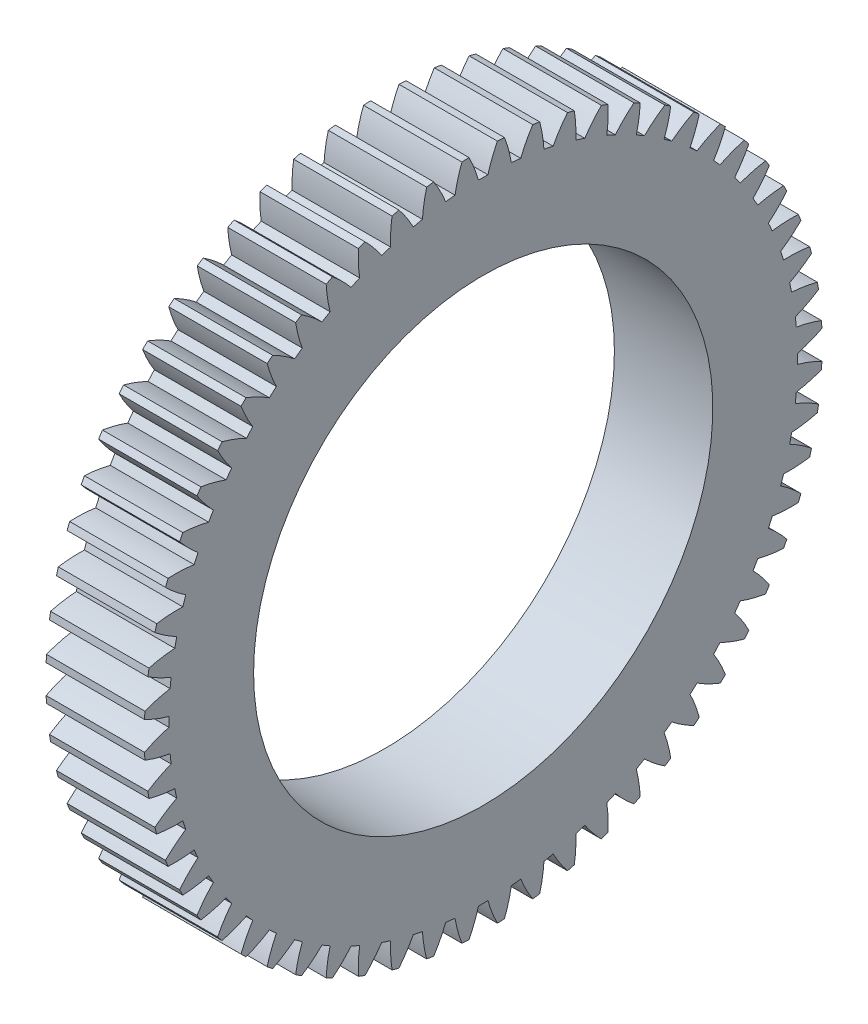
SolidWorks part; units mm, degrees
ref_plane "Plane1" through (0, 0, 0) normal (0, 0, 1) x (1, 0, 0)
ref_plane "Plane2" through (0, 0, 0) normal (0, 1, 0) x (1, 0, 0)
ref_plane "Plane3" through (0, 0, 0) normal (1, 0, 0) x (0, 0, -1)
sketch "HoldingSke" plane through (0, 0, 0) normal (0, 1, 0) x (1, 0, 0)
  line L0 (0, 0) -> (0.5, -0.866)
  line L1 (-15, 0) -> (100, 0) construction
  line L2 (0, 0) -> (-2.1039, 2.3779)
  line L3 (0, 0) -> (-11.863, 4.5341)
  line L4 (0, 0) -> (4.318, 7.479)
  line L5 (0, 0) -> (-46.8476, -17.4728)
  line L6 (0, 0) -> (-7.4607, -5.0337)
  line L7 (-2.1039, 2.3779) -> (8.6586, 51.2059)
  line L8 (-76.2, 54.61) -> (-72.9, 54.61)
  line L9 (-71.009, 38.7566) -> (-53.1078, 45.2721)
  line L10 (-76.2, 71.12) -> (104.1128, 71.12)
  line L11 (0, 0) -> (-9, 0)
  line L12 (-76.2, 101.6) -> (-76.162, 101.6)
  line L13 (24.9733, 27.94) -> (52.9518, 28.4284)
  line L14 (24.9733, 27.94) -> (24.9743, 27.94)
  line L15 (24.9733, 27.94) -> (100.4006, 29.5858)
  line L16 (-63.627, -1) -> (-12.827, -1)
  circle A0 centre (0, 0) radius 21
  circle A1 centre (0, 0) radius 28.749
  circle A2 centre (0, 0) radius 37.5
  circle A3 centre (0, 0) radius 21
  dimension "MHD" = 57.498
  dimension "Hub_dia" = 75
  dimension "Bore" = 42
  dimension "MBD" = 42
  dimension "Num_teeth" = 60
  dimension "Pitch" = 1
  dimension "Overall_len" = 50
  dimension "Show_teeth" = 60
  dimension "Thickness" = 9
  dimension "OAL" = 50.0001
  dimension "T_dim" = 3.3
  dimension "Ap" = 20
  dimension "H" = 19.05
  dimension "Pitch_radius" = 180.3128
  dimension "Width" = 9
  dimension "Backlash" = 0.038
  dimension "Addendum_fac" = 1
  dimension "Dedendum_fac" = 1.25
  dimension "Clearance_fac" = 0.25
  dimension "Dedendum_add" = 0.001
  dimension "Module" = 1
sketch "BasProSke" plane through (0, 0, 0) normal (0, 1, 0) x (1, 0, 0)
  line L0 (-10, 0) -> (60, 0) construction
  line L1 (0, 0) -> (0, 31)
  line L2 (0, 0) -> (9, 0)
  line L3 (9, 0) -> (9, 31)
  line L4 (9, 31) -> (0, 31)
  dimension "Thickness" = 9
  dimension "Diameter" = 62
revolve "Base-Revolve" add sketch "BasProSke" angle 360 about L0
sketch "TooCutSke" plane through (0, 0, 0) normal (1, 0, 0) x (0, 0, -1)
  line L1 (0, 0) -> (0, 107) construction
  line L2 (0, 0) -> (-0.8518, 29.9879) construction
  line L3 (0, 0) -> (-3.1393, 59.9006) construction
  line L4 (-0.8518, 29.9879) -> (-1.5696, 29.9503) construction
  arc A0 (0.4302, 28.7458) -> (-0.4302, 28.7458) centre (0, 0) ccw
  arc A1 (1.3127, 30.9976) -> (-1.3127, 30.9976) centre (0, 0) ccw
  circle A2 centre (0, 0) radius 30 construction
  circle A3 centre (0, 0) radius 28.1908 construction
  arc A4 (-0.4302, 28.7458) -> (-1.3127, 30.9976) centre (-11.9871, 25.5153) ccw
  arc A5 (1.3127, 30.9976) -> (0.4302, 28.7458) centre (11.9871, 25.5153) ccw
  dimension "Root_dia" = 57.498
  dimension "Overcut_dia" = 62.0508
  dimension "Pitch_dia" = 60
  dimension "Base_dia" = 56.3816
  dimension "Flank_rad" = 12
  dimension "Half_ang" = 3
  dimension "Half_CT" = 0.7188
extrude "ToothCut" cut sketch "TooCutSke" along normal through all
fillet "Breaks" [suppressed] radius 0.02
fillet "RootFillets" [suppressed] radius 0.251
pattern_circular "TeethCuts" count 60 every 6 about axis through (-10, 0, 0) along (1, 0, 0) of "ToothCut", "RootFillets", "Breaks"
sketch "HubNeaOneSke" plane through (0, 0, 0) normal (-1, 0, 0) x (0, 0, 1)
  circle A0 centre (0, 0) radius 28.749
  dimension "Diameter" = 57.498
extrude "HubNearOne" [suppressed] add sketch "HubNeaOneSke" along normal blind 41.0001
sketch "HubNeaBotSke" plane through (0, 0, 0) normal (-1, 0, 0) x (0, 0, 1)
  circle A0 centre (0, 0) radius 28.749
  dimension "Diameter" = 57.498
extrude "HubNearBoth" [suppressed] add sketch "HubNeaBotSke" along normal blind 20.5
ref_plane "FarPln" through (9, 0, 0) normal (1, 0, 0) x (0, 0, -1)
sketch "HubFarSke" plane through (9, 0, 0) normal (1, 0, 0) x (0, 0, -1)
  circle A0 centre (0, 0) radius 28.749
  dimension "Diameter" = 57.498
extrude "HubFar" [suppressed] add sketch "HubFarSke" along normal blind 20.5
sketch "BorSke" plane through (0, 0, 0) normal (1, 0, 0) x (0, 0, -1)
  circle A0 centre (0, 0) radius 21
  dimension "Diameter" = 42
extrude "Bore" cut sketch "BorSke" along normal mid plane 100.0001
sketch "KeySke" plane through (0, 0, 0) normal (1, 0, 0) x (0, 0, -1)
  line L0 (-6, 0) -> (-6, 24.3)
  line L1 (-6, 24.3) -> (6, 24.3)
  line L2 (6, 24.3) -> (6, 0)
  line L3 (0, 0) -> (0, 34) construction
  line L4 (-6, 0) -> (6, 0)
  dimension "Offset" = 24.3
  dimension "Width" = 12
extrude "Keyway" [suppressed] cut sketch "KeySke" along normal mid plane 100.0001
pattern_circular "Keyway2" [suppressed] count 2 every 90 about axis through (-10, 0, 0) along (1, 0, 0)
equation "' \"Module@HoldingSke\" = 6.35"
equation "' \"Num_teeth@HoldingSke\" = 12"
equation "' \"Ap@HoldingSke\" =  20"
equation "' \"Ap@HoldingSke\" = 20"
equation "' \"Width@HoldingSke\" = 0.5 * 25.4"
equation "' \"Hub_dia@HoldingSke\"= 1 * 25.4"
equation "' \"Hub_dia@HoldingSke\" = 1 * 25.4"
equation "' \"Overall_len@HoldingSke\" = 1.0 * 25.4"
equation "' \"Bore@HoldingSke\" = 0.75 * 25.4"
equation "' \"T_dim@HoldingSke\" = 0.1 * 25.4"
equation "' \"Width@KeySke\" = 0.25 * 25.4"
equation "' \"Show_teeth@HoldingSke\" = 13"
equation "' \"Backlash@HoldingSke\" = 0.009 * 25.4"
equation "' \"Addendum_fac@HoldingSke\" = 1.0"
equation "' \"Dedendum_fac@HoldingSke\" = 1.25"
equation "' \"Dedendum_add@HoldingSke\" = 0.00005 * 25.4"
equation "' \"Clearance_fac@HoldingSke\" = 0.25"
equation "\"Pitch@HoldingSke\" = 1 / \"Module@HoldingSke\""
equation "\"Overcut_dia@TooCutSke\" = (\"Num_teeth@HoldingSke\" + 2 * \"Addendum_fac@HoldingSke\") / \"Pitch@HoldingSke\" + 0.002 * 25.4"
equation "\"Pitch_dia@TooCutSke\" = \"Num_teeth@HoldingSke\" / \"Pitch@HoldingSke\""
equation "\"Base_dia@TooCutSke\" = \"Num_teeth@HoldingSke\" / \"Pitch@HoldingSke\" * cos((\"Ap@HoldingSke\"  * 3.14159265 / 180))"
equation "\"Root_dia@TooCutSke\" = (\"Num_teeth@HoldingSke\" + 2) / \"Pitch@HoldingSke\" - 2 * (\"Addendum_fac@HoldingSke\" + \"Dedendum_fac@HoldingSke\") / \"Pitch@HoldingSke\" - \"Dedendum_add@HoldingSke\" * 2"
equation "\"Half_ang@TooCutSke\" = 180 / \"Num_teeth@HoldingSke\""
equation "\"Half_CT@TooCutSke\" = \"Num_teeth@HoldingSke\" / \"Pitch@HoldingSke\" * sin((3.14159265 / 2 / \"Num_teeth@HoldingSke\")) / 2 - 7 * \"Backlash@HoldingSke\" / 4"
equation "\"Flank_rad@TooCutSke\" = \"Num_teeth@HoldingSke\" / \"Pitch@HoldingSke\" / 5"
equation "\"Radius@RootFillets\" = \"Clearance_fac@HoldingSke\" / \"Pitch@HoldingSke\" + \"Dedendum_add@HoldingSke\""
equation "\"Break_rad@Breaks\" = 0.02 / \"Pitch@HoldingSke\""
equation "\"Thickness@HoldingSke\" = \"Width@HoldingSke\""
equation "\"OAL@HoldingSke\" = \"Thickness@HoldingSke\""
equation "\"MHD@HoldingSke\" = (\"Num_teeth@HoldingSke\" + 2) / \"Pitch@HoldingSke\" - 2 * (\"Addendum_fac@HoldingSke\" + \"Dedendum_fac@HoldingSke\")  / \"Pitch@HoldingSke\" - \"Dedendum_add@HoldingSke\" * 2"
equation "\"MBD@HoldingSke\" = (\"Num_teeth@HoldingSke\" + 2) / \"Pitch@HoldingSke\" - 2 * (\"Addendum_fac@HoldingSke\" + \"Dedendum_fac@HoldingSke\")  / \"Pitch@HoldingSke\" - \"Dedendum_add@HoldingSke\" * 2 - 0.002 * 25.4"
equation "\"MHD@HoldingSke\" = ((sgn( \"MHD@HoldingSke\" - \"Hub_dia@HoldingSke\" )-1)*( \"MHD@HoldingSke\" - \"Hub_dia@HoldingSke\" ))/-2+ \"Hub_dia@HoldingSke\""
equation "\"MBD@HoldingSke\" = ((sgn( \"MBD@HoldingSke\" - \"Bore@HoldingSke\" )-1)*( \"MBD@HoldingSke\" - \"Bore@HoldingSke\" ))/-2+ \"Bore@HoldingSke\""
equation "\"OAL@HoldingSke\" = ((sgn( \"OAL@HoldingSke\" - \"Overall_len@HoldingSke\" )+1)*( \"OAL@HoldingSke\" - \"Overall_len@HoldingSke\" ))/2 + \"Overall_len@HoldingSke\" + 0.000002 * 25.4"
equation "\"Num_teeth@TeethCuts\" = int( \"Show_teeth@HoldingSke\" ) + 1"
equation "\"Num_teeth@TeethCuts\" = ((sgn( \"Num_teeth@TeethCuts\" - \"Num_teeth@HoldingSke\" )-1)*( \"Num_teeth@TeethCuts\" - \"Num_teeth@HoldingSke\" ))/-2+ \"Num_teeth@HoldingSke\""
equation "\"Num_teeth@TeethCuts\" = ((sgn( \"Num_teeth@TeethCuts\" - 2.0)+1)*( \"Num_teeth@TeethCuts\" - 2.0))/2 +2.0"
equation "\"Angle@TeethCuts\" = 360.0 / \"Num_teeth@HoldingSke\""
equation "\"Diameter@BasProSke\" = (\"Num_teeth@HoldingSke\" + 2 * \"Addendum_fac@HoldingSke\") / \"Pitch@HoldingSke\""
equation "\"Thickness@BasProSke\"  = \"Thickness@HoldingSke\""
equation "' \"Fillet_rad@BasProSke\" =  \"Thickness@HoldingSke\" * 0.05"
equation "' \"Fillet_rad@BasProSke\" = \"Thickness@HoldingSke\" * 0.05"
equation "\"MHD@HoldingSke\" = ((sgn( \"MHD@HoldingSke\" - \"Root_dia@TooCutSke\" )-1)*( \"MHD@HoldingSke\" - \"Root_dia@TooCutSke\" ))/-2+ \"Root_dia@TooCutSke\""
equation "\"Diameter@HubNeaOneSke\" = \"MHD@HoldingSke\""
equation "\"Length@HubNearOne\" = \"OAL@HoldingSke\" - \"Thickness@BasProSke\""
equation "\"Diameter@HubNeaBotSke\" = \"MHD@HoldingSke\""
equation "\"Length@HubNearBoth\" = ( \"OAL@HoldingSke\" - \"Thickness@BasProSke\" ) / 2.0"
equation "\"Thickness@FarPln\" = \"Thickness@BasProSke\""
equation "\"Diameter@HubFarSke\" = \"MHD@HoldingSke\""
equation "\"Length@HubFar\" = ( \"OAL@HoldingSke\" - \"Thickness@BasProSke\" ) / 2.0"
equation "\"Diameter@BorSke\" = \"MBD@HoldingSke\""
equation "\"D1@Bore\" = \"OAL@HoldingSke\" * 2.0"
equation "\"D1@Keyway\" = \"OAL@HoldingSke\" * 2.0"
equation "\"Offset@KeySke\" = \"T_dim@HoldingSke\" + \"MBD@HoldingSke\" / 2.0"
